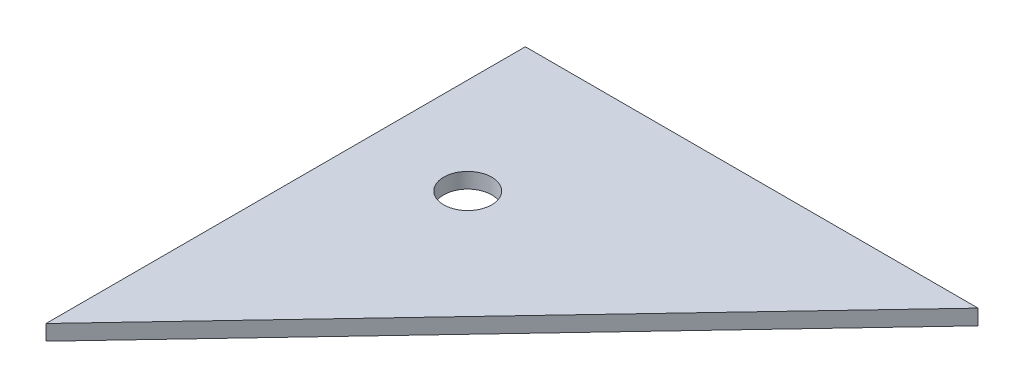
SolidWorks part; units mm, degrees
ref_plane "Front Plane" through (0, 0, 0) normal (0, 0, 1) x (1, 0, 0)
ref_plane "Top Plane" through (0, 0, 0) normal (0, 1, 0) x (1, 0, 0)
ref_plane "Right Plane" through (0, 0, 0) normal (1, 0, 0) x (0, 0, -1)
sketch "Sketch1" plane through (0, 0, 0) normal (0, 1, 0) x (1, 0, 0)
  line L0 (0, 0) -> (0, 79.2058)
  line L1 (0, 79.2058) -> (74.7965, 79.2058)
  line L2 (74.7965, 79.2058) -> (0, 0)
  line L3 (-12.1464, 5.635) -> (67.0207, 89.469) construction
  line L4 (-37.1365, 60.4576) -> (-35.1445, 60.4118) construction
  line L5 (108.6662, 66.5058) -> (-47.6794, 66.5058) construction
  circle A0 centre (15.875, 53.8058) radius 3.9688
  circle A1 centre (15.875, 53.8058) radius 10.16 construction
  dimension "D3" = 7.9375
  dimension "D8" = 20.32
  dimension "D4" = 12.7
  dimension "D1" = 15.875
  dimension "D2" = 46.64
  dimension "D5" = 12.7
  dimension "D6" = 12.7
  dimension "D7" = 12.7
extrude "Boss-Extrude1" add sketch "Sketch1" along normal blind 2.54
